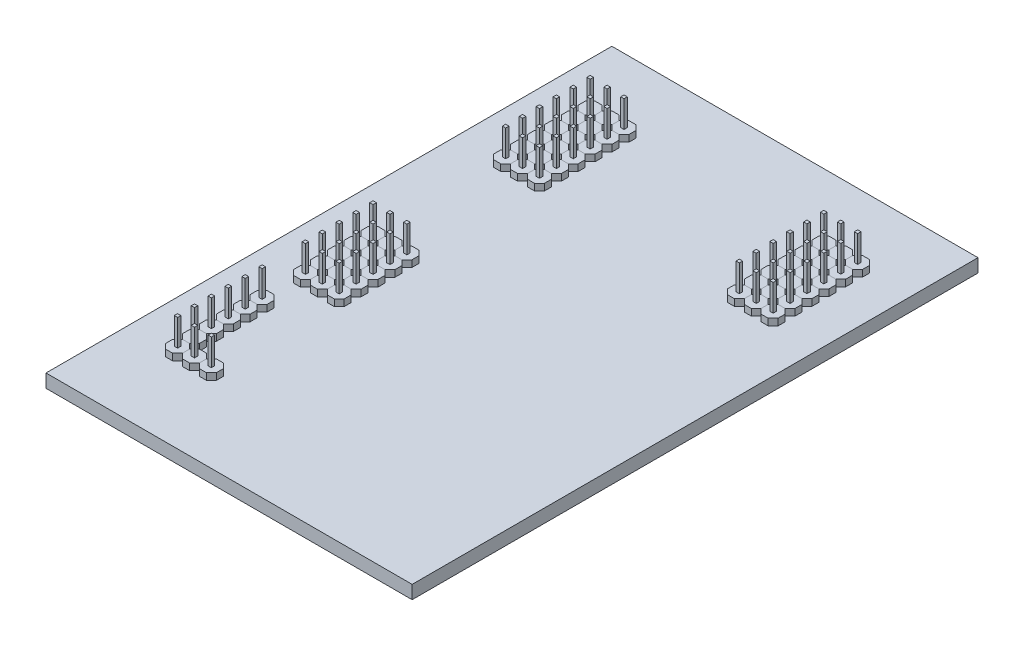
SolidWorks part; units mm, degrees
material "uhlíková ocel 7850"
ref_plane "Přední rovina" through (0, 0, 0) normal (0, 0, 1) x (1, 0, 0)
ref_plane "Horní rovina" through (0, 0, 0) normal (0, 1, 0) x (1, 0, 0)
ref_plane "Pravá rovina" through (0, 0, 0) normal (1, 0, 0) x (0, 0, -1)
sketch "Skica1" plane through (0, 0, 0) normal (0, 1, 0) x (1, 0, 0)
  line L1 (27.5, -42.5) -> (-27.5, -42.5)
  line L2 (27.5, -42.5) -> (27.5, 42.5)
  line L3 (27.5, 42.5) -> (-27.5, 42.5)
  line L4 (-27.5, -42.5) -> (-27.5, 42.5)
  line L5 (27.5, -42.5) -> (-27.5, 42.5) construction
  line L6 (27.5, 42.5) -> (-27.5, -42.5) construction
  point P0 (0, 0)
  dimension "D1" = 55
  dimension "D2" = 85
extrude "Přidat vysunutím1" add sketch "Skica1" along normal blind 2
sketch "Skica2" plane through (0, 2, 0) normal (0, 1, 0) x (1, 0, 0)
  line L0 (-23.495, -16.1739) -> (-24.765, -16.1739) construction
  line L1 (-19.564, -16.1739) -> (-20.6161, -16.1739)
  line L2 (-20.6161, -16.1739) -> (-21.36, -16.9179)
  line L3 (-21.36, -16.9179) -> (-21.36, -17.97)
  line L4 (-21.36, -17.97) -> (-20.6161, -18.7139)
  line L5 (-20.6161, -18.7139) -> (-19.564, -18.7139)
  line L6 (-19.564, -18.7139) -> (-18.82, -17.97)
  line L7 (-18.82, -17.97) -> (-18.82, -16.9179)
  line L8 (-18.82, -16.9179) -> (-19.564, -16.1739)
  line L9 (-24.765, -18.7139) -> (-23.495, -18.7139) construction
  line L10 (-22.86, -16.8089) -> (-22.86, -18.0789) construction
  circle A0 centre (-20.09, -17.4439) radius 1.27 construction
  dimension "D1" = 1.5
extrude "Přidat vysunutím2" add sketch "Skica2" along normal blind 1 separate body
sketch "Skica3" plane through (0, 3, 0) normal (0, 1, 0) x (1, 0, 0)
  line L0 (-20.09, -16.1739) -> (-20.09, -17.4439) construction
  line L1 (-20.34, -17.6939) -> (-19.84, -17.6939)
  line L2 (-20.34, -17.6939) -> (-20.34, -17.1939)
  line L3 (-20.34, -17.1939) -> (-19.84, -17.1939)
  line L4 (-19.84, -17.6939) -> (-19.84, -17.1939)
  line L5 (-20.34, -17.6939) -> (-19.84, -17.1939) construction
  line L6 (-20.34, -17.1939) -> (-19.84, -17.6939) construction
  line L7 (-19.564, -16.1739) -> (-20.6161, -16.1739) construction
  line L8 (-20.09, -17.4439) -> (-21.36, -17.4439) construction
  line L10 (-21.36, -16.9179) -> (-21.36, -17.97) construction
  point P0 (-20.09, -17.4439)
  dimension "D1" = 0.5
extrude "Přidat vysunutím3" add sketch "Skica3" along normal blind 4
pattern_linear "LinPole1" count 6 spacing 2.54 along (0, 0, 1) of bodies 107
pattern_linear "LinPole2" count 3 spacing 2.54 along (1, 0, 0) of bodies 112
pattern_linear "LinPole3" count 2 spacing 6.5 along (0, 0, -1) of bodies 107
pattern_linear "LinPole4" count 3 spacing 2.54 along (1, 0, 0) of bodies 115
pattern_linear "LinPole5" count 5 spacing 2.54 along (0, 0, -1) of bodies 115 116 117
pattern_linear "LinPole6" count 2 spacing 25 along (0, 0, -1) of bodies 127 123 119 120 124 125 121 128 129
pattern_linear "LinPole7" count 2 spacing 7.62 along (0, 0, -1) of bodies 132 131 130 137 134 133 136 135 138
mirror "Zrcadlit1" about plane through (0, 0, 0) normal (1, 0, 0) of bodies 138 131 144 137 130 143 136 142 135 141 134 147 140 133 146 139 132 145
